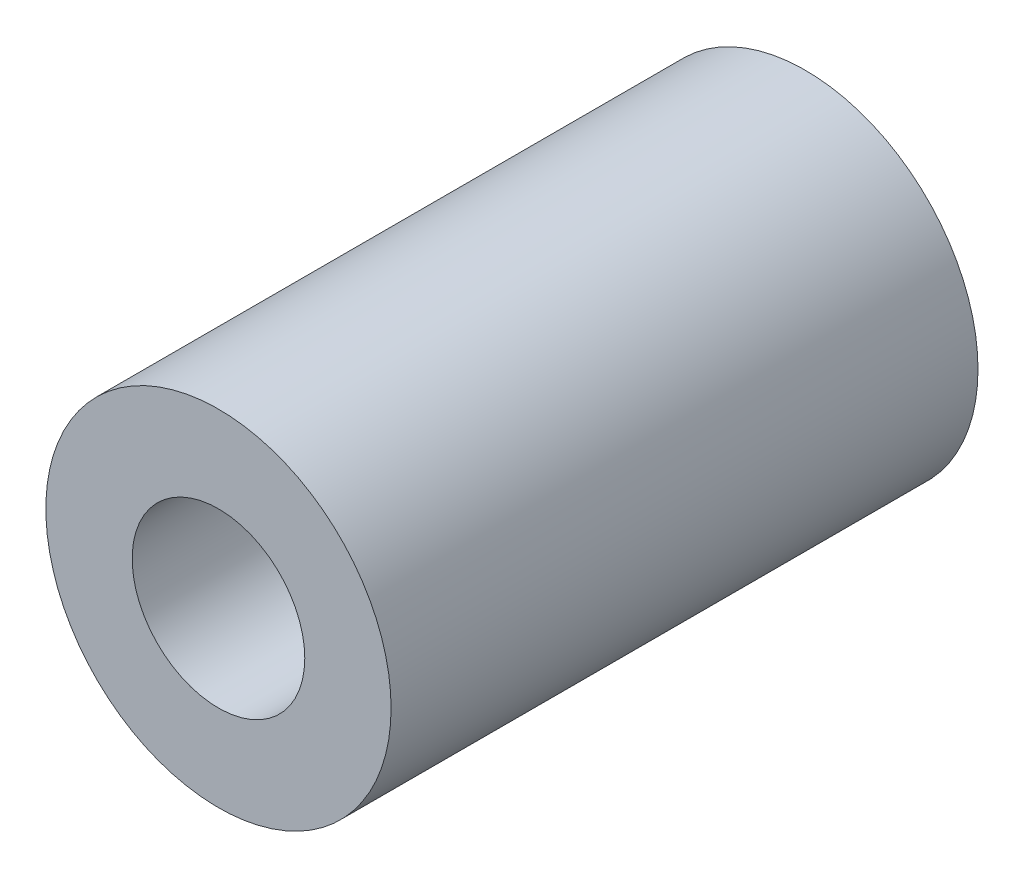
SolidWorks part; units mm, degrees
ref_plane "正面" through (0, 0, 0) normal (0, 0, 1) x (1, 0, 0)
ref_plane "平面" through (0, 0, 0) normal (0, 1, 0) x (1, 0, 0)
ref_plane "右側面" through (0, 0, 0) normal (1, 0, 0) x (0, 0, -1)
sketch "ｽｹｯﾁ1" plane through (0, 0, 0) normal (0, 0, 1) x (1, 0, 0)
  circle A0 centre (0, 0) radius 5
  circle A1 centre (0, 0) radius 2.5
  dimension "D1" = 10
  dimension "D2" = 5
extrude "ﾎﾞｽ - 押し出し1" add sketch "ｽｹｯﾁ1" along normal blind 17
